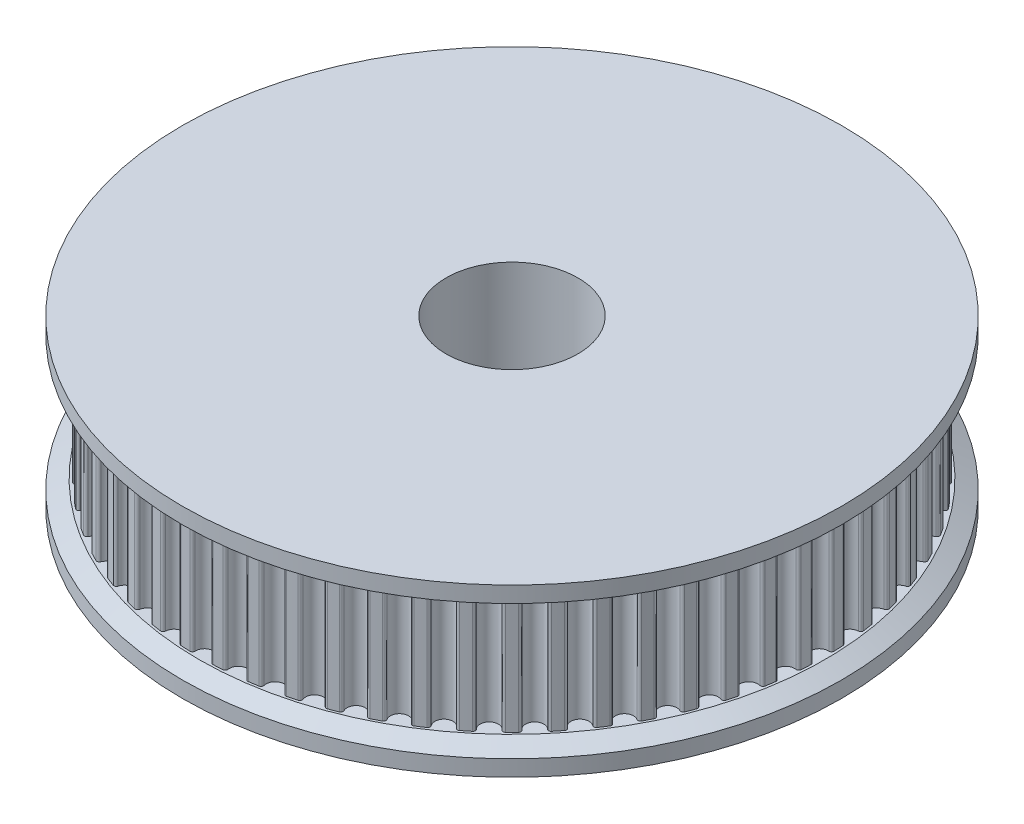
SolidWorks part; units mm, degrees
material "1060 Сплав"
ref_plane "Спереди" through (0, 0, 0) normal (0, 0, 1) x (1, 0, 0)
ref_plane "Сверху" through (0, 0, 0) normal (0, 1, 0) x (1, 0, 0)
ref_plane "Справа" through (0, 0, 0) normal (1, 0, 0) x (0, 0, -1)
other "Configuration Table"
sketch "Эскиз1" plane through (0, 0, 0) normal (0, 1, 0) x (1, 0, 0)
  circle A0 centre (0, 0) radius 10
  circle A1 centre (0, 0) radius 4
  dimension "D1" = 20
  dimension "D2" = 8
extrude "Бобышка-Вытянуть1" add sketch "Эскиз1" along normal blind 7.45
sketch "Эскиз2" plane through (0, 7.45, 0) normal (0, 1, 0) x (1, 0, 0)
  arc A1 (1.2682, 18.8073) -> (0.7046, 18.8368) centre (0, 0) ccw
  arc A3 (-0.5492, 18.679) -> (0.5492, 18.679) centre (0, 18.65) ccw
  arc A74 (-0.5492, 18.679) -> (-0.7046, 18.8368) centre (-0.699, 18.6869) ccw
  arc A77 (0.5492, 18.679) -> (0.7046, 18.8368) centre (0.699, 18.6869) cw
  arc A82 (-0.7046, 18.8368) -> (-1.2682, 18.8073) centre (0, 0) ccw
  arc A83 (1.4063, 18.6341) -> (2.4987, 18.5193) centre (1.9495, 18.5478) ccw
  arc A84 (1.4063, 18.6341) -> (1.2682, 18.8073) centre (1.2581, 18.6576) ccw
  arc A85 (2.4987, 18.5193) -> (2.6698, 18.66) centre (2.6485, 18.5115) cw
  arc A86 (3.3464, 18.385) -> (4.4208, 18.1566) centre (3.8776, 18.2425) ccw
  arc A87 (3.3464, 18.385) -> (3.2272, 18.5717) centre (3.2015, 18.4239) ccw
  arc A88 (4.4208, 18.1566) -> (4.6056, 18.2787) centre (4.569, 18.1332) cw
  arc A89 (5.2498, 17.9345) -> (6.2945, 17.5951) centre (5.7632, 17.7372) ccw
  arc A90 (5.2498, 17.9345) -> (5.1508, 18.1326) centre (5.1098, 17.9883) ccw
  arc A91 (6.2945, 17.5951) -> (6.491, 17.6971) centre (6.4394, 17.5563) cw
  arc A92 (7.0957, 17.2875) -> (8.0992, 16.8407) centre (7.5856, 17.0376) ccw
  arc A93 (7.0957, 17.2875) -> (7.0179, 17.4949) centre (6.9621, 17.3557) ccw
  arc A94 (8.0992, 16.8407) -> (8.3053, 16.9217) centre (8.2393, 16.787) cw
  arc A95 (8.8639, 16.4511) -> (9.8152, 15.9019) centre (9.325, 16.1514) ccw
  arc A96 (8.8639, 16.4511) -> (8.8082, 16.6655) centre (8.7381, 16.5329) ccw
  arc A97 (9.8152, 15.9019) -> (10.0286, 15.9609) centre (9.9488, 15.8338) cw
  arc A98 (10.5349, 15.4345) -> (11.4236, 14.7888) centre (10.9622, 15.0882) ccw
  arc A99 (10.5349, 15.4345) -> (10.5019, 15.6535) centre (10.4184, 15.5289) ccw
  arc A100 (11.4236, 14.7888) -> (11.6421, 14.8251) centre (11.5494, 14.7072) cw
  arc A101 (12.0905, 14.2487) -> (12.9069, 13.5137) centre (12.4793, 13.8597) ccw
  arc A102 (12.0905, 14.2487) -> (12.0807, 14.47) centre (11.9845, 14.3548) ccw
  arc A103 (12.9069, 13.5137) -> (13.1279, 13.527) centre (13.0235, 13.4194) cw
  arc A104 (13.5137, 12.9069) -> (14.2487, 12.0905) centre (13.8597, 12.4793) ccw
  arc A105 (13.5137, 12.9069) -> (13.527, 13.1279) centre (13.4194, 13.0235) ccw
  arc A106 (14.2487, 12.0905) -> (14.47, 12.0807) centre (14.3548, 11.9845) cw
  arc A107 (14.7888, 11.4236) -> (15.4345, 10.5349) centre (15.0882, 10.9622) ccw
  arc A108 (14.7888, 11.4236) -> (14.8251, 11.6421) centre (14.7072, 11.5494) ccw
  arc A109 (15.4345, 10.5349) -> (15.6535, 10.5019) centre (15.5289, 10.4184) cw
  arc A110 (15.9019, 9.8152) -> (16.4511, 8.8639) centre (16.1514, 9.325) ccw
  arc A111 (15.9019, 9.8152) -> (15.9609, 10.0286) centre (15.8338, 9.9488) ccw
  arc A112 (16.4511, 8.8639) -> (16.6655, 8.8082) centre (16.5329, 8.7381) cw
  arc A113 (16.8407, 8.0992) -> (17.2875, 7.0957) centre (17.0376, 7.5856) ccw
  arc A114 (16.8407, 8.0992) -> (16.9217, 8.3053) centre (16.787, 8.2393) ccw
  arc A115 (17.2875, 7.0957) -> (17.4949, 7.0179) centre (17.3557, 6.9621) cw
  arc A116 (17.5951, 6.2945) -> (17.9345, 5.2498) centre (17.7372, 5.7632) ccw
  arc A117 (17.5951, 6.2945) -> (17.6971, 6.491) centre (17.5563, 6.4394) ccw
  arc A118 (17.9345, 5.2498) -> (18.1326, 5.1508) centre (17.9883, 5.1098) cw
  arc A119 (18.1566, 4.4208) -> (18.385, 3.3464) centre (18.2425, 3.8776) ccw
  arc A120 (18.1566, 4.4208) -> (18.2787, 4.6056) centre (18.1332, 4.569) ccw
  arc A121 (18.385, 3.3464) -> (18.5717, 3.2272) centre (18.4239, 3.2015) cw
  arc A122 (18.5193, 2.4987) -> (18.6341, 1.4063) centre (18.5478, 1.9495) ccw
  arc A123 (18.5193, 2.4987) -> (18.66, 2.6698) centre (18.5115, 2.6485) ccw
  arc A124 (18.6341, 1.4063) -> (18.8073, 1.2682) centre (18.6576, 1.2581) cw
  arc A125 (18.679, 0.5492) -> (18.679, -0.5492) centre (18.65, 0) ccw
  arc A126 (18.679, 0.5492) -> (18.8368, 0.7046) centre (18.6869, 0.699) ccw
  arc A127 (18.679, -0.5492) -> (18.8368, -0.7046) centre (18.6869, -0.699) cw
  arc A128 (18.6341, -1.4063) -> (18.5193, -2.4987) centre (18.5478, -1.9495) ccw
  arc A129 (18.6341, -1.4063) -> (18.8073, -1.2682) centre (18.6576, -1.2581) ccw
  arc A130 (18.5193, -2.4987) -> (18.66, -2.6698) centre (18.5115, -2.6485) cw
  arc A131 (18.385, -3.3464) -> (18.1566, -4.4208) centre (18.2425, -3.8776) ccw
  arc A132 (18.385, -3.3464) -> (18.5717, -3.2272) centre (18.4239, -3.2015) ccw
  arc A133 (18.1566, -4.4208) -> (18.2787, -4.6056) centre (18.1332, -4.569) cw
  arc A134 (17.9345, -5.2498) -> (17.5951, -6.2945) centre (17.7372, -5.7632) ccw
  arc A135 (17.9345, -5.2498) -> (18.1326, -5.1508) centre (17.9883, -5.1098) ccw
  arc A136 (17.5951, -6.2945) -> (17.6971, -6.491) centre (17.5563, -6.4394) cw
  arc A137 (17.2875, -7.0957) -> (16.8407, -8.0992) centre (17.0376, -7.5856) ccw
  arc A138 (17.2875, -7.0957) -> (17.4949, -7.0179) centre (17.3557, -6.9621) ccw
  arc A139 (16.8407, -8.0992) -> (16.9217, -8.3053) centre (16.787, -8.2393) cw
  arc A140 (16.4511, -8.8639) -> (15.9019, -9.8152) centre (16.1514, -9.325) ccw
  arc A141 (16.4511, -8.8639) -> (16.6655, -8.8082) centre (16.5329, -8.7381) ccw
  arc A142 (15.9019, -9.8152) -> (15.9609, -10.0286) centre (15.8338, -9.9488) cw
  arc A143 (15.4345, -10.5349) -> (14.7888, -11.4236) centre (15.0882, -10.9622) ccw
  arc A144 (15.4345, -10.5349) -> (15.6535, -10.5019) centre (15.5289, -10.4184) ccw
  arc A145 (14.7888, -11.4236) -> (14.8251, -11.6421) centre (14.7072, -11.5494) cw
  arc A146 (14.2487, -12.0905) -> (13.5137, -12.9069) centre (13.8597, -12.4793) ccw
  arc A147 (14.2487, -12.0905) -> (14.47, -12.0807) centre (14.3548, -11.9845) ccw
  arc A148 (13.5137, -12.9069) -> (13.527, -13.1279) centre (13.4194, -13.0235) cw
  arc A149 (12.9069, -13.5137) -> (12.0905, -14.2487) centre (12.4793, -13.8597) ccw
  arc A150 (12.9069, -13.5137) -> (13.1279, -13.527) centre (13.0235, -13.4194) ccw
  arc A151 (12.0905, -14.2487) -> (12.0807, -14.47) centre (11.9845, -14.3548) cw
  arc A152 (11.4236, -14.7888) -> (10.5349, -15.4345) centre (10.9622, -15.0882) ccw
  arc A153 (11.4236, -14.7888) -> (11.6421, -14.8251) centre (11.5494, -14.7072) ccw
  arc A154 (10.5349, -15.4345) -> (10.5019, -15.6535) centre (10.4184, -15.5289) cw
  arc A155 (9.8152, -15.9019) -> (8.8639, -16.4511) centre (9.325, -16.1514) ccw
  arc A156 (9.8152, -15.9019) -> (10.0286, -15.9609) centre (9.9488, -15.8338) ccw
  arc A157 (8.8639, -16.4511) -> (8.8082, -16.6655) centre (8.7381, -16.5329) cw
  arc A158 (8.0992, -16.8407) -> (7.0957, -17.2875) centre (7.5856, -17.0376) ccw
  arc A159 (8.0992, -16.8407) -> (8.3053, -16.9217) centre (8.2393, -16.787) ccw
  arc A160 (7.0957, -17.2875) -> (7.0179, -17.4949) centre (6.9621, -17.3557) cw
  arc A161 (6.2945, -17.5951) -> (5.2498, -17.9345) centre (5.7632, -17.7372) ccw
  arc A162 (6.2945, -17.5951) -> (6.491, -17.6971) centre (6.4394, -17.5563) ccw
  arc A163 (5.2498, -17.9345) -> (5.1508, -18.1326) centre (5.1098, -17.9883) cw
  arc A164 (4.4208, -18.1566) -> (3.3464, -18.385) centre (3.8776, -18.2425) ccw
  arc A165 (4.4208, -18.1566) -> (4.6056, -18.2787) centre (4.569, -18.1332) ccw
  arc A166 (3.3464, -18.385) -> (3.2272, -18.5717) centre (3.2015, -18.4239) cw
  arc A167 (2.4987, -18.5193) -> (1.4063, -18.6341) centre (1.9495, -18.5478) ccw
  arc A168 (2.4987, -18.5193) -> (2.6698, -18.66) centre (2.6485, -18.5115) ccw
  arc A169 (1.4063, -18.6341) -> (1.2682, -18.8073) centre (1.2581, -18.6576) cw
  arc A170 (0.5492, -18.679) -> (-0.5492, -18.679) centre (0, -18.65) ccw
  arc A171 (0.5492, -18.679) -> (0.7046, -18.8368) centre (0.699, -18.6869) ccw
  arc A172 (-0.5492, -18.679) -> (-0.7046, -18.8368) centre (-0.699, -18.6869) cw
  arc A173 (-1.4063, -18.6341) -> (-2.4987, -18.5193) centre (-1.9495, -18.5478) ccw
  arc A174 (-1.4063, -18.6341) -> (-1.2682, -18.8073) centre (-1.2581, -18.6576) ccw
  arc A175 (-2.4987, -18.5193) -> (-2.6698, -18.66) centre (-2.6485, -18.5115) cw
  arc A176 (-3.3464, -18.385) -> (-4.4208, -18.1566) centre (-3.8776, -18.2425) ccw
  arc A177 (-3.3464, -18.385) -> (-3.2272, -18.5717) centre (-3.2015, -18.4239) ccw
  arc A178 (-4.4208, -18.1566) -> (-4.6056, -18.2787) centre (-4.569, -18.1332) cw
  arc A179 (-5.2498, -17.9345) -> (-6.2945, -17.5951) centre (-5.7632, -17.7372) ccw
  arc A180 (-5.2498, -17.9345) -> (-5.1508, -18.1326) centre (-5.1098, -17.9883) ccw
  arc A181 (-6.2945, -17.5951) -> (-6.491, -17.6971) centre (-6.4394, -17.5563) cw
  arc A182 (-7.0957, -17.2875) -> (-8.0992, -16.8407) centre (-7.5856, -17.0376) ccw
  arc A183 (-7.0957, -17.2875) -> (-7.0179, -17.4949) centre (-6.9621, -17.3557) ccw
  arc A184 (-8.0992, -16.8407) -> (-8.3053, -16.9217) centre (-8.2393, -16.787) cw
  arc A185 (-8.8639, -16.4511) -> (-9.8152, -15.9019) centre (-9.325, -16.1514) ccw
  arc A186 (-8.8639, -16.4511) -> (-8.8082, -16.6655) centre (-8.7381, -16.5329) ccw
  arc A187 (-9.8152, -15.9019) -> (-10.0286, -15.9609) centre (-9.9488, -15.8338) cw
  arc A188 (-10.5349, -15.4345) -> (-11.4236, -14.7888) centre (-10.9622, -15.0882) ccw
  arc A189 (-10.5349, -15.4345) -> (-10.5019, -15.6535) centre (-10.4184, -15.5289) ccw
  arc A190 (-11.4236, -14.7888) -> (-11.6421, -14.8251) centre (-11.5494, -14.7072) cw
  arc A191 (-12.0905, -14.2487) -> (-12.9069, -13.5137) centre (-12.4793, -13.8597) ccw
  arc A192 (-12.0905, -14.2487) -> (-12.0807, -14.47) centre (-11.9845, -14.3548) ccw
  arc A193 (-12.9069, -13.5137) -> (-13.1279, -13.527) centre (-13.0235, -13.4194) cw
  arc A194 (-13.5137, -12.9069) -> (-14.2487, -12.0905) centre (-13.8597, -12.4793) ccw
  arc A195 (-13.5137, -12.9069) -> (-13.527, -13.1279) centre (-13.4194, -13.0235) ccw
  arc A196 (-14.2487, -12.0905) -> (-14.47, -12.0807) centre (-14.3548, -11.9845) cw
  arc A197 (-14.7888, -11.4236) -> (-15.4345, -10.5349) centre (-15.0882, -10.9622) ccw
  arc A198 (-14.7888, -11.4236) -> (-14.8251, -11.6421) centre (-14.7072, -11.5494) ccw
  arc A199 (-15.4345, -10.5349) -> (-15.6535, -10.5019) centre (-15.5289, -10.4184) cw
  arc A200 (-15.9019, -9.8152) -> (-16.4511, -8.8639) centre (-16.1514, -9.325) ccw
  arc A201 (-15.9019, -9.8152) -> (-15.9609, -10.0286) centre (-15.8338, -9.9488) ccw
  arc A202 (-16.4511, -8.8639) -> (-16.6655, -8.8082) centre (-16.5329, -8.7381) cw
  arc A203 (-16.8407, -8.0992) -> (-17.2875, -7.0957) centre (-17.0376, -7.5856) ccw
  arc A204 (-16.8407, -8.0992) -> (-16.9217, -8.3053) centre (-16.787, -8.2393) ccw
  arc A205 (-17.2875, -7.0957) -> (-17.4949, -7.0179) centre (-17.3557, -6.9621) cw
  arc A206 (-17.5951, -6.2945) -> (-17.9345, -5.2498) centre (-17.7372, -5.7632) ccw
  arc A207 (-17.5951, -6.2945) -> (-17.6971, -6.491) centre (-17.5563, -6.4394) ccw
  arc A208 (-17.9345, -5.2498) -> (-18.1326, -5.1508) centre (-17.9883, -5.1098) cw
  arc A209 (-18.1566, -4.4208) -> (-18.385, -3.3464) centre (-18.2425, -3.8776) ccw
  arc A210 (-18.1566, -4.4208) -> (-18.2787, -4.6056) centre (-18.1332, -4.569) ccw
  arc A211 (-18.385, -3.3464) -> (-18.5717, -3.2272) centre (-18.4239, -3.2015) cw
  arc A212 (-18.5193, -2.4987) -> (-18.6341, -1.4063) centre (-18.5478, -1.9495) ccw
  arc A213 (-18.5193, -2.4987) -> (-18.66, -2.6698) centre (-18.5115, -2.6485) ccw
  arc A214 (-18.6341, -1.4063) -> (-18.8073, -1.2682) centre (-18.6576, -1.2581) cw
  arc A215 (-18.679, -0.5492) -> (-18.679, 0.5492) centre (-18.65, 0) ccw
  arc A216 (-18.679, -0.5492) -> (-18.8368, -0.7046) centre (-18.6869, -0.699) ccw
  arc A217 (-18.679, 0.5492) -> (-18.8368, 0.7046) centre (-18.6869, 0.699) cw
  arc A218 (-18.6341, 1.4063) -> (-18.5193, 2.4987) centre (-18.5478, 1.9495) ccw
  arc A219 (-18.6341, 1.4063) -> (-18.8073, 1.2682) centre (-18.6576, 1.2581) ccw
  arc A220 (-18.5193, 2.4987) -> (-18.66, 2.6698) centre (-18.5115, 2.6485) cw
  arc A221 (-18.385, 3.3464) -> (-18.1566, 4.4208) centre (-18.2425, 3.8776) ccw
  arc A222 (-18.385, 3.3464) -> (-18.5717, 3.2272) centre (-18.4239, 3.2015) ccw
  arc A223 (-18.1566, 4.4208) -> (-18.2787, 4.6056) centre (-18.1332, 4.569) cw
  arc A224 (-17.9345, 5.2498) -> (-17.5951, 6.2945) centre (-17.7372, 5.7632) ccw
  arc A225 (-17.9345, 5.2498) -> (-18.1326, 5.1508) centre (-17.9883, 5.1098) ccw
  arc A226 (-17.5951, 6.2945) -> (-17.6971, 6.491) centre (-17.5563, 6.4394) cw
  arc A227 (-17.2875, 7.0957) -> (-16.8407, 8.0992) centre (-17.0376, 7.5856) ccw
  arc A228 (-17.2875, 7.0957) -> (-17.4949, 7.0179) centre (-17.3557, 6.9621) ccw
  arc A229 (-16.8407, 8.0992) -> (-16.9217, 8.3053) centre (-16.787, 8.2393) cw
  arc A230 (-16.4511, 8.8639) -> (-15.9019, 9.8152) centre (-16.1514, 9.325) ccw
  arc A231 (-16.4511, 8.8639) -> (-16.6655, 8.8082) centre (-16.5329, 8.7381) ccw
  arc A232 (-15.9019, 9.8152) -> (-15.9609, 10.0286) centre (-15.8338, 9.9488) cw
  arc A233 (-15.4345, 10.5349) -> (-14.7888, 11.4236) centre (-15.0882, 10.9622) ccw
  arc A234 (-15.4345, 10.5349) -> (-15.6535, 10.5019) centre (-15.5289, 10.4184) ccw
  arc A235 (-14.7888, 11.4236) -> (-14.8251, 11.6421) centre (-14.7072, 11.5494) cw
  arc A236 (-14.2487, 12.0905) -> (-13.5137, 12.9069) centre (-13.8597, 12.4793) ccw
  arc A237 (-14.2487, 12.0905) -> (-14.47, 12.0807) centre (-14.3548, 11.9845) ccw
  arc A238 (-13.5137, 12.9069) -> (-13.527, 13.1279) centre (-13.4194, 13.0235) cw
  arc A239 (-12.9069, 13.5137) -> (-12.0905, 14.2487) centre (-12.4793, 13.8597) ccw
  arc A240 (-12.9069, 13.5137) -> (-13.1279, 13.527) centre (-13.0235, 13.4194) ccw
  arc A241 (-12.0905, 14.2487) -> (-12.0807, 14.47) centre (-11.9845, 14.3548) cw
  arc A242 (-11.4236, 14.7888) -> (-10.5349, 15.4345) centre (-10.9622, 15.0882) ccw
  arc A243 (-11.4236, 14.7888) -> (-11.6421, 14.8251) centre (-11.5494, 14.7072) ccw
  arc A244 (-10.5349, 15.4345) -> (-10.5019, 15.6535) centre (-10.4184, 15.5289) cw
  arc A245 (-9.8152, 15.9019) -> (-8.8639, 16.4511) centre (-9.325, 16.1514) ccw
  arc A246 (-9.8152, 15.9019) -> (-10.0286, 15.9609) centre (-9.9488, 15.8338) ccw
  arc A247 (-8.8639, 16.4511) -> (-8.8082, 16.6655) centre (-8.7381, 16.5329) cw
  arc A248 (-8.0992, 16.8407) -> (-7.0957, 17.2875) centre (-7.5856, 17.0376) ccw
  arc A249 (-8.0992, 16.8407) -> (-8.3053, 16.9217) centre (-8.2393, 16.787) ccw
  arc A250 (-7.0957, 17.2875) -> (-7.0179, 17.4949) centre (-6.9621, 17.3557) cw
  arc A251 (-6.2945, 17.5951) -> (-5.2498, 17.9345) centre (-5.7632, 17.7372) ccw
  arc A252 (-6.2945, 17.5951) -> (-6.491, 17.6971) centre (-6.4394, 17.5563) ccw
  arc A253 (-5.2498, 17.9345) -> (-5.1508, 18.1326) centre (-5.1098, 17.9883) cw
  arc A254 (-4.4208, 18.1566) -> (-3.3464, 18.385) centre (-3.8776, 18.2425) ccw
  arc A255 (-4.4208, 18.1566) -> (-4.6056, 18.2787) centre (-4.569, 18.1332) ccw
  arc A256 (-3.3464, 18.385) -> (-3.2272, 18.5717) centre (-3.2015, 18.4239) cw
  arc A257 (-2.4987, 18.5193) -> (-1.4063, 18.6341) centre (-1.9495, 18.5478) ccw
  arc A258 (-2.4987, 18.5193) -> (-2.6698, 18.66) centre (-2.6485, 18.5115) ccw
  arc A259 (-1.4063, 18.6341) -> (-1.2682, 18.8073) centre (-1.2581, 18.6576) cw
  arc A260 (3.2272, 18.5717) -> (2.6698, 18.66) centre (0, 0) ccw
  arc A261 (5.1508, 18.1326) -> (4.6056, 18.2787) centre (0, 0) ccw
  arc A262 (7.0179, 17.4949) -> (6.491, 17.6971) centre (0, 0) ccw
  arc A263 (8.8082, 16.6655) -> (8.3053, 16.9217) centre (0, 0) ccw
  arc A264 (10.5019, 15.6535) -> (10.0286, 15.9609) centre (0, 0) ccw
  arc A265 (12.0807, 14.47) -> (11.6421, 14.8251) centre (0, 0) ccw
  arc A266 (13.527, 13.1279) -> (13.1279, 13.527) centre (0, 0) ccw
  arc A267 (14.8251, 11.6421) -> (14.47, 12.0807) centre (0, 0) ccw
  arc A268 (15.9609, 10.0286) -> (15.6535, 10.5019) centre (0, 0) ccw
  arc A269 (16.9217, 8.3053) -> (16.6655, 8.8082) centre (0, 0) ccw
  arc A270 (18.5717, -3.2272) -> (18.66, -2.6698) centre (0, 0) ccw
  arc A271 (18.8073, -1.2682) -> (18.8368, -0.7046) centre (0, 0) ccw
  arc A272 (18.8368, 0.7046) -> (18.8073, 1.2682) centre (0, 0) ccw
  arc A273 (18.66, 2.6698) -> (18.5717, 3.2272) centre (0, 0) ccw
  arc A274 (18.2787, 4.6056) -> (18.1326, 5.1508) centre (0, 0) ccw
  arc A275 (17.6971, 6.491) -> (17.4949, 7.0179) centre (0, 0) ccw
  arc A276 (14.47, -12.0807) -> (14.8251, -11.6421) centre (0, 0) ccw
  arc A277 (15.6535, -10.5019) -> (15.9609, -10.0286) centre (0, 0) ccw
  arc A278 (16.6655, -8.8082) -> (16.9217, -8.3053) centre (0, 0) ccw
  arc A279 (17.4949, -7.0179) -> (17.6971, -6.491) centre (0, 0) ccw
  arc A280 (18.1326, -5.1508) -> (18.2787, -4.6056) centre (0, 0) ccw
  arc A281 (2.6698, -18.66) -> (3.2272, -18.5717) centre (0, 0) ccw
  arc A282 (4.6056, -18.2787) -> (5.1508, -18.1326) centre (0, 0) ccw
  arc A283 (6.491, -17.6971) -> (7.0179, -17.4949) centre (0, 0) ccw
  arc A284 (8.3053, -16.9217) -> (8.8082, -16.6655) centre (0, 0) ccw
  arc A285 (10.0286, -15.9609) -> (10.5019, -15.6535) centre (0, 0) ccw
  arc A286 (11.6421, -14.8251) -> (12.0807, -14.47) centre (0, 0) ccw
  arc A287 (13.1279, -13.527) -> (13.527, -13.1279) centre (0, 0) ccw
  arc A288 (-7.0179, -17.4949) -> (-6.491, -17.6971) centre (0, 0) ccw
  arc A289 (-5.1508, -18.1326) -> (-4.6056, -18.2787) centre (0, 0) ccw
  arc A290 (-3.2272, -18.5717) -> (-2.6698, -18.66) centre (0, 0) ccw
  arc A291 (-1.2682, -18.8073) -> (-0.7046, -18.8368) centre (0, 0) ccw
  arc A292 (0.7046, -18.8368) -> (1.2682, -18.8073) centre (0, 0) ccw
  arc A293 (-16.9217, -8.3053) -> (-16.6655, -8.8082) centre (0, 0) ccw
  arc A294 (-15.9609, -10.0286) -> (-15.6535, -10.5019) centre (0, 0) ccw
  arc A295 (-14.8251, -11.6421) -> (-14.47, -12.0807) centre (0, 0) ccw
  arc A296 (-13.527, -13.1279) -> (-13.1279, -13.527) centre (0, 0) ccw
  arc A297 (-12.0807, -14.47) -> (-11.6421, -14.8251) centre (0, 0) ccw
  arc A298 (-10.5019, -15.6535) -> (-10.0286, -15.9609) centre (0, 0) ccw
  arc A299 (-8.8082, -16.6655) -> (-8.3053, -16.9217) centre (0, 0) ccw
  arc A300 (-17.6971, -6.491) -> (-17.4949, -7.0179) centre (0, 0) ccw
  arc A301 (-18.2787, -4.6056) -> (-18.1326, -5.1508) centre (0, 0) ccw
  arc A302 (-18.66, -2.6698) -> (-18.5717, -3.2272) centre (0, 0) ccw
  arc A303 (-18.8368, -0.7046) -> (-18.8073, -1.2682) centre (0, 0) ccw
  arc A304 (-18.8073, 1.2682) -> (-18.8368, 0.7046) centre (0, 0) ccw
  arc A305 (-18.5717, 3.2272) -> (-18.66, 2.6698) centre (0, 0) ccw
  arc A306 (-18.1326, 5.1508) -> (-18.2787, 4.6056) centre (0, 0) ccw
  arc A307 (-17.4949, 7.0179) -> (-17.6971, 6.491) centre (0, 0) ccw
  arc A308 (-16.6655, 8.8082) -> (-16.9217, 8.3053) centre (0, 0) ccw
  arc A309 (-15.6535, 10.5019) -> (-15.9609, 10.0286) centre (0, 0) ccw
  arc A310 (-14.47, 12.0807) -> (-14.8251, 11.6421) centre (0, 0) ccw
  arc A311 (-13.1279, 13.527) -> (-13.527, 13.1279) centre (0, 0) ccw
  arc A312 (-11.6421, 14.8251) -> (-12.0807, 14.47) centre (0, 0) ccw
  arc A313 (-10.0286, 15.9609) -> (-10.5019, 15.6535) centre (0, 0) ccw
  arc A314 (-8.3053, 16.9217) -> (-8.8082, 16.6655) centre (0, 0) ccw
  arc A315 (-6.491, 17.6971) -> (-7.0179, 17.4949) centre (0, 0) ccw
  arc A316 (-4.6056, 18.2787) -> (-5.1508, 18.1326) centre (0, 0) ccw
  arc A317 (-2.6698, 18.66) -> (-3.2272, 18.5717) centre (0, 0) ccw
  circle A318 centre (0, 0) radius 4 construction
  circle A319 centre (0, 0) radius 4
  point P426 (0, 0)
  dimension "D1" = 37.7
  dimension "D2" = 0.2
  dimension "D3" = 0.55
  dimension "D4" = 0.15
extrude "Бобышка-Вытянуть2" add sketch "Эскиз2" along normal blind 7
sketch "Эскиз3" plane through (0, 14.45, 0) normal (0, 1, 0) x (1, 0, 0)
  circle A3 centre (0, 0) radius 20
  circle A4 centre (0, 0) radius 4 construction
  circle A5 centre (0, 0) radius 4
  dimension "D1" = 40
extrude "Бобышка-Вытянуть3" add sketch "Эскиз3" along normal blind 1.55
sketch "Эскиз4" plane through (0, 0, 0) normal (0, 0, 1) x (1, 0, 0)
  line L0 (-10, 3.725) -> (10, 3.725) construction
  line L1 (-10, 7.45) -> (-10, 0) construction
  line L2 (10, 0) -> (10, 7.45) construction
  circle A0 centre (0, 3.725) radius 1.5
  dimension "D1" = 3
extrude "Вырез-Вытянуть1" cut sketch "Эскиз4" along normal up to surface (9.8869 mm away)
sketch "Эскиз5" plane through (0, 0, 0) normal (1, 0, 0) x (0, 0, -1)
  line L0 (10, 3.725) -> (-9.8869, 3.725) construction
  line L1 (10, 0) -> (10, 7.45) construction
  circle A0 centre (0, 3.725) radius 1.5
  spline S1 degree 2 poles (-10, 5.225) (-9.775, 3.725) (-10, 2.225) knots 0 0 0 1 1 1 weights 0.0085 0.01 0.0115 construction
  dimension "D1" = 3
extrude "Вырез-Вытянуть2" cut sketch "Эскиз5" along normal up to surface (9.8869 mm away)
sketch "Эскиз7" plane through (0, 7.45, 0) normal (0, -1, 0) x (1, 0, 0)
  circle A0 centre (0, 0) radius 20 construction
  circle A1 centre (0, 0) radius 20
  circle A2 centre (0, 0) radius 4 construction
  circle A3 centre (0, 0) radius 4
extrude "Бобышка-Вытянуть4" add sketch "Эскиз7" along normal blind 1.55
sketch "Эскиз6" plane through (0, 7.45, 0) normal (0, 1, 0) x (1, 0, 0)
  circle A0 centre (0, 0) radius 18.1
  arc A3 (-16.9217, -8.3053) -> (-16.6655, -8.8082) centre (0, 0) ccw construction
  dimension "D1" = 0.75
  dimension "D2" = 36.2
chamfer "Фаска1" distance 1 angle 30 2 edges at (0, 14.45, 20) (0, 7.45, -20)
